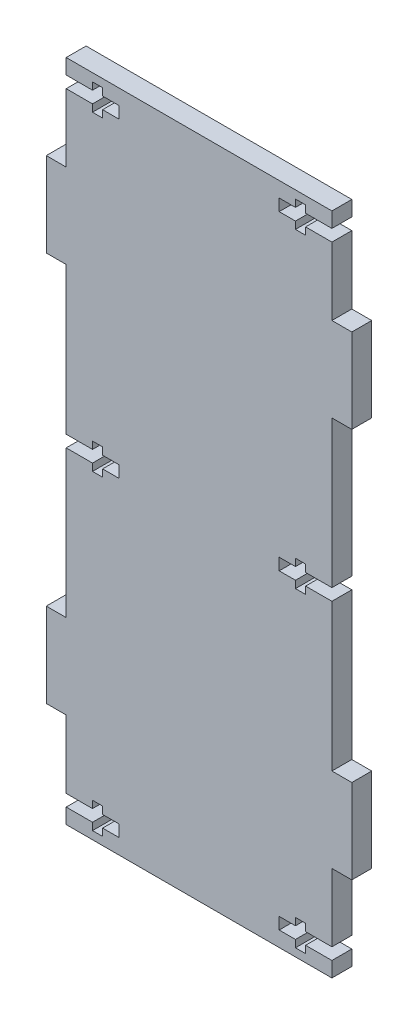
SolidWorks part; units mm, degrees
ref_plane "Front Plane" through (0, 0, 0) normal (0, 0, 1) x (1, 0, 0)
ref_plane "Top Plane" through (0, 0, 0) normal (0, 1, 0) x (1, 0, 0)
ref_plane "Right Plane" through (0, 0, 0) normal (1, 0, 0) x (0, 0, -1)
sketch "Sketch1" plane through (0, 0, 0) normal (0, 0, 1) x (1, 0, 0)
  line L1 (0, 0) -> (80.01, 0)
  line L2 (0, 0) -> (0, 200.025)
  line L3 (0, 200.025) -> (80.01, 200.025)
  line L4 (80.01, 0) -> (80.01, 200.025)
  dimension "D1" = 80.01
  dimension "D2" = 200.025
extrude "Boss-Extrude1" add sketch "Sketch1" against normal blind 5.9944
sketch "Sketch2" plane through (0, 0, 0) normal (0, 0, 1) x (1, 0, 0)
  line L0 (80.01, 0) -> (80.01, 200.025) construction
  line L1 (80.01, 171.45) -> (86.0044, 171.45)
  line L2 (80.01, 171.45) -> (80.01, 146.05)
  line L3 (80.01, 146.05) -> (86.0044, 146.05)
  line L4 (86.0044, 171.45) -> (86.0044, 146.05)
  line L5 (80.01, 200.025) -> (0, 200.025) construction
  line L6 (40.005, 200.025) -> (40.005, 0) construction
  line L7 (0, 0) -> (80.01, 0) construction
  line L8 (0, 100.0125) -> (80.01, 100.0125) construction
  line L9 (0, 200.025) -> (0, 0) construction
  line L22 (0, 146.05) -> (-5.9944, 146.05)
  line L23 (-5.9944, 171.45) -> (-5.9944, 146.05)
  line L24 (0, 171.45) -> (-5.9944, 171.45)
  line L25 (0, 171.45) -> (0, 146.05)
  line L26 (0, 28.575) -> (0, 53.975)
  line L27 (0, 28.575) -> (-5.9944, 28.575)
  line L28 (-5.9944, 28.575) -> (-5.9944, 53.975)
  line L29 (0, 53.975) -> (-5.9944, 53.975)
  line L30 (80.01, 53.975) -> (86.0044, 53.975)
  line L31 (86.0044, 28.575) -> (86.0044, 53.975)
  line L32 (80.01, 28.575) -> (86.0044, 28.575)
  line L33 (80.01, 28.575) -> (80.01, 53.975)
  dimension "D1" = 28.575
  dimension "D2" = 25.4
  dimension "D3" = 5.9944
extrude "Boss-Extrude2" add sketch "Sketch2" against normal blind 5.9944
sketch "Sketch3" plane through (0, 0, 0) normal (0, 0, 1) x (1, 0, 0)
  line L0 (80.01, 171.45) -> (80.01, 200.025) construction
  line L1 (80.01, 195.453) -> (72.0852, 195.453)
  line L2 (80.01, 195.453) -> (80.01, 191.897)
  line L3 (80.01, 191.897) -> (72.0852, 191.897)
  line L4 (64.135, 195.453) -> (64.135, 191.897)
  line L5 (72.0852, 195.453) -> (72.0852, 197.6374)
  line L6 (72.0852, 197.6374) -> (69.0372, 197.6374)
  line L7 (69.0372, 197.6374) -> (69.0372, 195.453)
  line L8 (64.135, 193.675) -> (80.01, 193.675) construction
  line L9 (69.0372, 195.453) -> (64.135, 195.453)
  line L10 (72.0852, 191.897) -> (72.0852, 189.7126)
  line L11 (72.0852, 189.7126) -> (69.0372, 189.7126)
  line L12 (69.0372, 189.7126) -> (69.0372, 191.897)
  line L13 (69.0372, 191.897) -> (64.135, 191.897)
  line L14 (40.005, 200.025) -> (40.005, 0) construction
  line L15 (80.01, 200.025) -> (0, 200.025) construction
  line L16 (0, 0) -> (80.01, 0) construction
  line L17 (0, 100.0125) -> (80.01, 100.0125) construction
  line L18 (0, 146.05) -> (0, 53.975) construction
  line L19 (80.01, 53.975) -> (80.01, 146.05) construction
  line L20 (64.135, 6.35) -> (80.01, 6.35) construction
  line L21 (69.0372, 8.128) -> (64.135, 8.128)
  line L22 (69.0372, 10.3124) -> (69.0372, 8.128)
  line L23 (72.0852, 10.3124) -> (69.0372, 10.3124)
  line L24 (72.0852, 8.128) -> (72.0852, 10.3124)
  line L25 (69.0372, 4.572) -> (64.135, 4.572)
  line L26 (69.0372, 2.3876) -> (69.0372, 4.572)
  line L27 (72.0852, 2.3876) -> (69.0372, 2.3876)
  line L28 (72.0852, 4.572) -> (72.0852, 2.3876)
  line L29 (64.135, 4.572) -> (64.135, 8.128)
  line L30 (80.01, 8.128) -> (72.0852, 8.128)
  line L31 (80.01, 4.572) -> (80.01, 8.128)
  line L32 (80.01, 4.572) -> (72.0852, 4.572)
  line L33 (69.0372, 96.0501) -> (69.0372, 98.2345)
  line L34 (69.0372, 103.9749) -> (69.0372, 101.7905)
  line L35 (72.0852, 103.9749) -> (69.0372, 103.9749)
  line L36 (80.01, 101.7905) -> (72.0852, 101.7905)
  line L37 (72.0852, 98.2345) -> (72.0852, 96.0501)
  line L38 (69.0372, 101.7905) -> (64.135, 101.7905)
  line L39 (80.01, 98.2345) -> (72.0852, 98.2345)
  line L40 (72.0852, 101.7905) -> (72.0852, 103.9749)
  line L41 (72.0852, 96.0501) -> (69.0372, 96.0501)
  line L42 (80.01, 101.7905) -> (80.01, 98.2345)
  line L43 (64.135, 101.7905) -> (64.135, 98.2345)
  line L44 (69.0372, 98.2345) -> (64.135, 98.2345)
  line L45 (10.9728, 10.3124) -> (10.9728, 8.128)
  line L46 (7.9248, 10.3124) -> (10.9728, 10.3124)
  line L47 (7.9248, 8.128) -> (7.9248, 10.3124)
  line L48 (0, 8.128) -> (7.9248, 8.128)
  line L49 (0, 4.572) -> (0, 8.128)
  line L50 (0, 4.572) -> (7.9248, 4.572)
  line L51 (7.9248, 4.572) -> (7.9248, 2.3876)
  line L52 (7.9248, 2.3876) -> (10.9728, 2.3876)
  line L53 (10.9728, 2.3876) -> (10.9728, 4.572)
  line L54 (10.9728, 4.572) -> (15.875, 4.572)
  line L55 (15.875, 4.572) -> (15.875, 8.128)
  line L56 (10.9728, 8.128) -> (15.875, 8.128)
  line L57 (7.9248, 96.0501) -> (10.9728, 96.0501)
  line L58 (7.9248, 98.2345) -> (7.9248, 96.0501)
  line L59 (0, 98.2345) -> (7.9248, 98.2345)
  line L60 (0, 101.7905) -> (0, 98.2345)
  line L61 (0, 101.7905) -> (7.9248, 101.7905)
  line L62 (7.9248, 101.7905) -> (7.9248, 103.9749)
  line L63 (7.9248, 103.9749) -> (10.9728, 103.9749)
  line L64 (10.9728, 103.9749) -> (10.9728, 101.7905)
  line L65 (10.9728, 101.7905) -> (15.875, 101.7905)
  line L66 (15.875, 101.7905) -> (15.875, 98.2345)
  line L67 (10.9728, 98.2345) -> (15.875, 98.2345)
  line L68 (10.9728, 96.0501) -> (10.9728, 98.2345)
  line L69 (0, 195.453) -> (7.9248, 195.453)
  line L70 (7.9248, 195.453) -> (7.9248, 197.6374)
  line L71 (7.9248, 197.6374) -> (10.9728, 197.6374)
  line L72 (10.9728, 197.6374) -> (10.9728, 195.453)
  line L73 (10.9728, 195.453) -> (15.875, 195.453)
  line L74 (15.875, 195.453) -> (15.875, 191.897)
  line L75 (10.9728, 191.897) -> (15.875, 191.897)
  line L76 (10.9728, 189.7126) -> (10.9728, 191.897)
  line L77 (7.9248, 189.7126) -> (10.9728, 189.7126)
  line L78 (7.9248, 191.897) -> (7.9248, 189.7126)
  line L79 (0, 191.897) -> (7.9248, 191.897)
  line L80 (0, 195.453) -> (0, 191.897)
  dimension "D1" = 3.556
  dimension "D2" = 15.875
  dimension "D3" = 3.048
  dimension "D4" = 3.9624
  dimension "D5" = 7.9248
  dimension "D6" = 6.35
extrude "Cut-Extrude1" cut sketch "Sketch3" against normal through all
